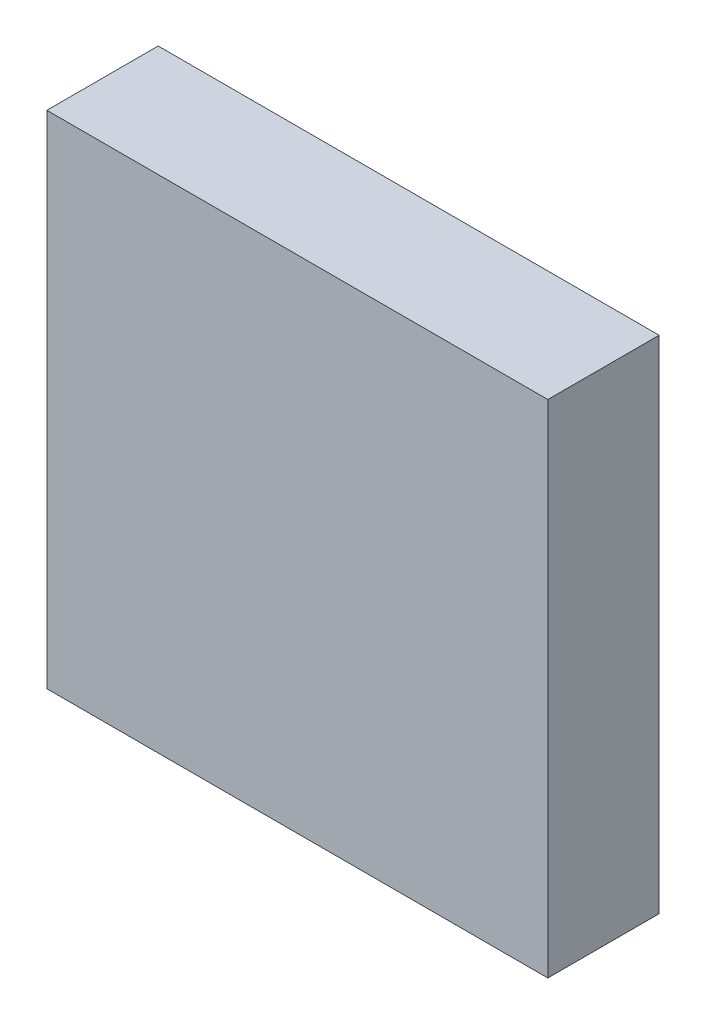
SolidWorks part; units mm, degrees
ref_plane "Alzado" through (0, 0, 0) normal (0, 0, 1) x (1, 0, 0)
ref_plane "Planta" through (0, 0, 0) normal (0, 1, 0) x (1, 0, 0)
ref_plane "Vista lateral" through (0, 0, 0) normal (1, 0, 0) x (0, 0, -1)
sketch "Croquis2" plane through (0, 0, 0) normal (0, 0, 1) x (1, 0, 0)
  line L1 (225, -225) -> (-225, -225)
  line L2 (225, -225) -> (225, 225)
  line L3 (225, 225) -> (-225, 225)
  line L4 (-225, -225) -> (-225, 225)
  line L5 (225, -225) -> (-225, 225) construction
  line L6 (225, 225) -> (-225, -225) construction
  point P0 (0, 0)
  dimension "D1" = 450
  dimension "D2" = 450
extrude "Saliente-Extruir1" add sketch "Croquis2" along normal blind 100
sketch "Croquis3" plane through (0, 0, 0) normal (0, 0, -1) x (-1, 0, 0)
  line L0 (-98.5976, 50.2985) -> (262.7358, 50.2985) construction
sketch "Croquis4" plane through (0, 0, 0) normal (0, 0, -1) x (-1, 0, 0)
  line L0 (151.0906, -171.9988) -> (180.424, -171.9988) construction
  line L1 (42.7612, -174.4988) -> (72.7612, -174.4988) construction
  line L2 (-62.3329, -169.7864) -> (-34.9996, -169.7864) construction
  line L3 (-168.9728, 118.3035) -> (-139.6395, 118.3035) construction
  line L4 (-67.0911, 129.2903) -> (-37.0911, 129.2903) construction
  line L5 (38.3593, 125.0093) -> (67.026, 125.0093) construction
sketch "Croquis5" plane through (225, 0, 0) normal (1, 0, 0) x (0, 0, -1)
  line L0 (-47.0734, 56.8168) -> (86.2599, 56.8168) construction
  line L1 (-28.9677, -129.8016) -> (199.0323, -129.8016) construction
sketch "Croquis6" plane through (0, -225, 0) normal (0, -1, 0) x (1, 0, 0)
  line L0 (-122.3025, -9.5594) -> (11.0309, -9.5594) construction
sketch "Croquis7" plane through (0, 0, 0) normal (0, 0, -1) x (-1, 0, 0)
  line L0 (-134.2679, 42.5415) -> (5.0654, 42.5415) construction
  line L1 (-123.0352, -180.8363) -> (-93.7019, -180.8363) construction
  line L2 (-6.0591, -178.9469) -> (22.6075, -178.9469) construction
  line L3 (98.1912, -178.6128) -> (128.1912, -178.6128) construction
